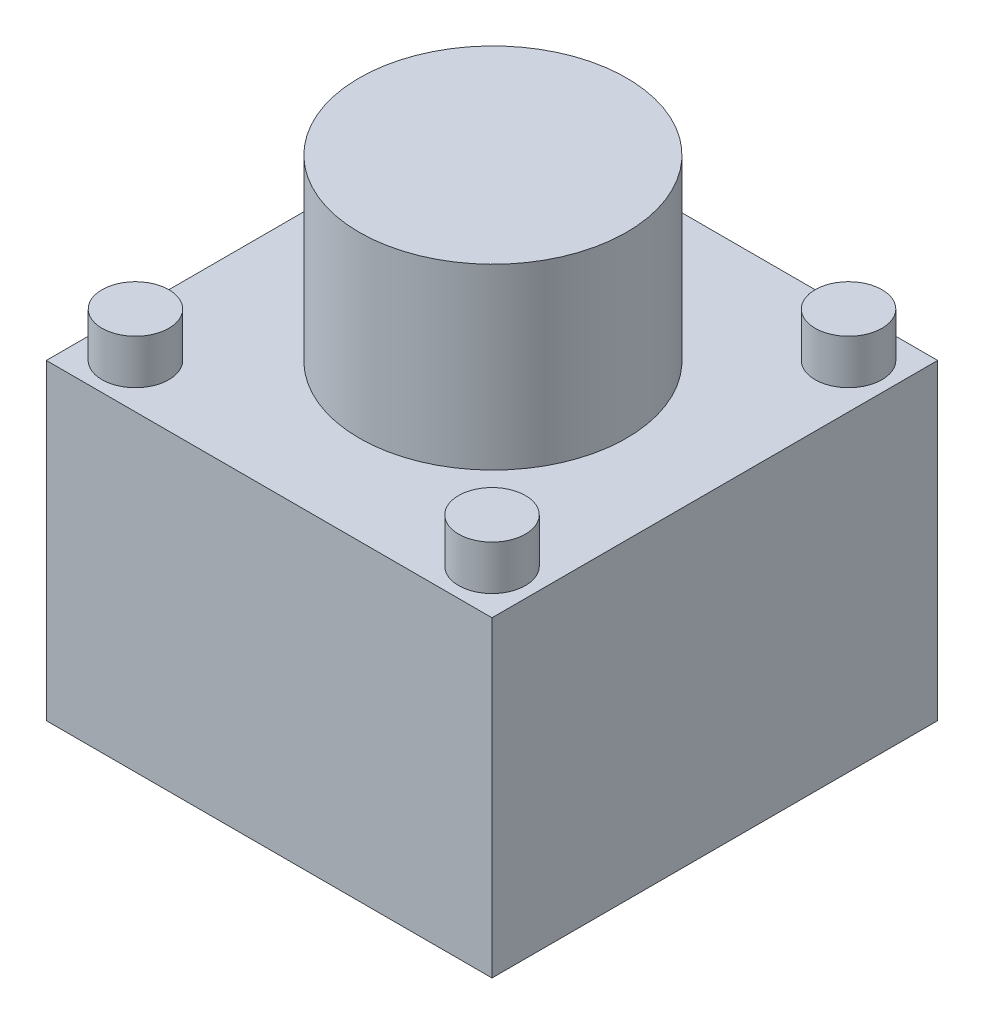
SolidWorks part; units mm, degrees
ref_plane "Front Plane" through (0, 0, 0) normal (0, 0, 1) x (1, 0, 0)
ref_plane "Top Plane" through (0, 0, 0) normal (0, 1, 0) x (1, 0, 0)
ref_plane "Right Plane" through (0, 0, 0) normal (1, 0, 0) x (0, 0, -1)
sketch "Sketch1" plane through (0, 0, 0) normal (0, 1, 0) x (1, 0, 0)
  line L1 (-8.1089, 4.5693) -> (1.8911, 4.5693)
  line L2 (-8.1089, 4.5693) -> (-8.1089, -5.4307)
  line L3 (-8.1089, -5.4307) -> (1.8911, -5.4307)
  line L4 (1.8911, 4.5693) -> (1.8911, -5.4307)
  dimension "D1" = 10
  dimension "D2" = 10
extrude "Boss-Extrude1" add sketch "Sketch1" along normal blind 7
sketch "Sketch2" plane through (0, 0, 5.4307) normal (0, 0, 1) x (1, 0, 0)
  line L0 (-6.1089, 7) -> (0.7218, 10)
  line L1 (-8.1089, 7) -> (1.8911, 7) construction
  line L2 (0.7218, 10) -> (-0.1089, 7)
  line L3 (-0.1089, 7) -> (-6.1089, 7)
  dimension "D1" = 2
  dimension "D2" = 2
  dimension "D3" = 3
sketch "Sketch3" plane through (0, 7, 0) normal (0, 1, 0) x (1, 0, 0)
  line L0 (-8.1089, 4.5693) -> (-8.1089, -5.4307) construction
  line L1 (1.8911, 4.5693) -> (-8.1089, 4.5693) construction
  line L2 (-8.1089, -5.4307) -> (1.8911, -5.4307) construction
  line L3 (1.8911, -5.4307) -> (1.8911, 4.5693) construction
  line L4 (0.7218, -5.4307) -> (-0.1089, -5.4307) construction
  circle A1 centre (-7.1089, 3.5693) radius 0.75
  circle A2 centre (-7.1089, -4.4307) radius 0.75
  circle A3 centre (0.8911, -4.4307) radius 0.75
  circle A4 centre (0.8911, 3.5693) radius 0.75
  dimension "D2" = 1.5
  dimension "D3" = 1.5
  dimension "D4" = 1.5
  dimension "D5" = 1.5
  dimension "D6" = 1
  dimension "D8" = 1
  dimension "D10" = 1
  dimension "D12" = 1
  dimension "D13" = 1
  dimension "D7" = 1
  dimension "D9" = 1
  dimension "1" = 1
  dimension "D11" = 1
extrude "Boss-Extrude2" add sketch "Sketch3" along normal blind 1
sketch "Sketch4" plane through (0, 7, 0) normal (0, 1, 0) x (1, 0, 0)
  line L0 (1.8911, 4.5693) -> (-8.1089, 4.5693) construction
  circle A0 centre (-3.0886, -0.4307) radius 3
  dimension "D1" = 6
  dimension "D2" = 5
extrude "Boss-Extrude4" add sketch "Sketch4" along normal blind 4
